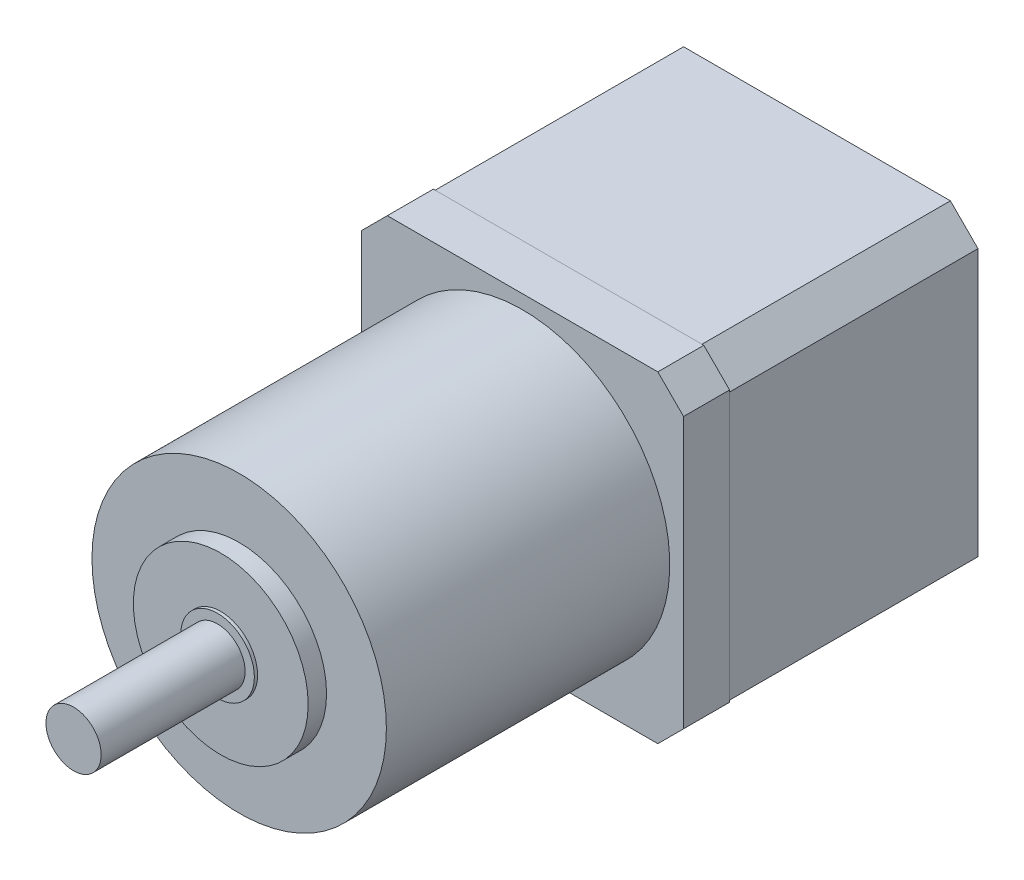
SolidWorks part; units mm, degrees
ref_plane "Front Plane" through (0, 0, 0) normal (0, 0, 1) x (1, 0, 0)
ref_plane "Top Plane" through (0, 0, 0) normal (0, 1, 0) x (1, 0, 0)
ref_plane "Right Plane" through (0, 0, 0) normal (1, 0, 0) x (0, 0, -1)
sketch "Sketch1" plane through (0, 0, 0) normal (0, 0, 1) x (1, 0, 0)
  line L1 (-17.5, 17.5) -> (17.5, 17.5)
  line L2 (-17.5, 17.5) -> (-17.5, -17.5)
  line L3 (-17.5, -17.5) -> (17.5, -17.5)
  line L4 (17.5, 17.5) -> (17.5, -17.5)
  line L5 (-17.5, 17.5) -> (17.5, -17.5) construction
  line L6 (-17.5, -17.5) -> (17.5, 17.5) construction
  point P0 (0, 0)
  dimension "D1" = 35
  dimension "D2" = 35
extrude "Boss-Extrude1" add sketch "Sketch1" along normal blind 27
chamfer "Chamfer1" distance 3 angle 45 4 edges at (-17.5, -17.5, 13.5) (17.5, -17.5, 13.5) (-17.5, 17.5, 13.5) (17.5, 17.5, 13.5)
sketch "Sketch2" plane through (0, 0, 27) normal (0, 0, 1) x (1, 0, 0)
  line L1 (-17.5, -17.5) -> (17.5, -17.5)
  line L2 (-17.5, -17.5) -> (-17.5, 17.5)
  line L3 (-17.5, 17.5) -> (17.5, 17.5)
  line L4 (17.5, -17.5) -> (17.5, 17.5)
  line L5 (-17.5, -17.5) -> (17.5, 17.5) construction
  line L6 (-17.5, 17.5) -> (17.5, -17.5) construction
  point P0 (0, 0)
  dimension "D1" = 35
  dimension "D2" = 35
extrude "Boss-Extrude2" add sketch "Sketch2" along normal blind 5 separate body
chamfer "Chamfer2" distance 2.8 angle 45 4 edges at (-17.5, -17.5, 29.5) (17.5, -17.5, 29.5) (-17.5, 17.5, 29.5) (17.5, 17.5, 29.5)
sketch "Sketch3" plane through (0, 0, 32) normal (0, 0, 1) x (1, 0, 0)
  circle A0 centre (0, 0) radius 16
  dimension "D1" = 32
extrude "Boss-Extrude3" add sketch "Sketch3" along normal blind 30.8
sketch "Sketch4" plane through (0, 0, 62.8) normal (0, 0, 1) x (1, 0, 0)
  circle A0 centre (0, 0) radius 9.5
  dimension "D1" = 19
extrude "Boss-Extrude4" add sketch "Sketch4" along normal blind 2
sketch "Sketch6" plane through (0, 0, 62.8) normal (0, 0, 1) x (1, 0, 0)
  circle A0 centre (0, 0) radius 3
  dimension "D1" = 6
extrude "Boss-Extrude5" add sketch "Sketch6" along normal blind 18
sketch "Sketch7" plane through (0, 0, 64.8) normal (0, 0, 1) x (1, 0, 0)
  circle A0 centre (0, 0) radius 4
  dimension "D1" = 8
extrude "Boss-Extrude6" add sketch "Sketch7" along normal blind 0.35
